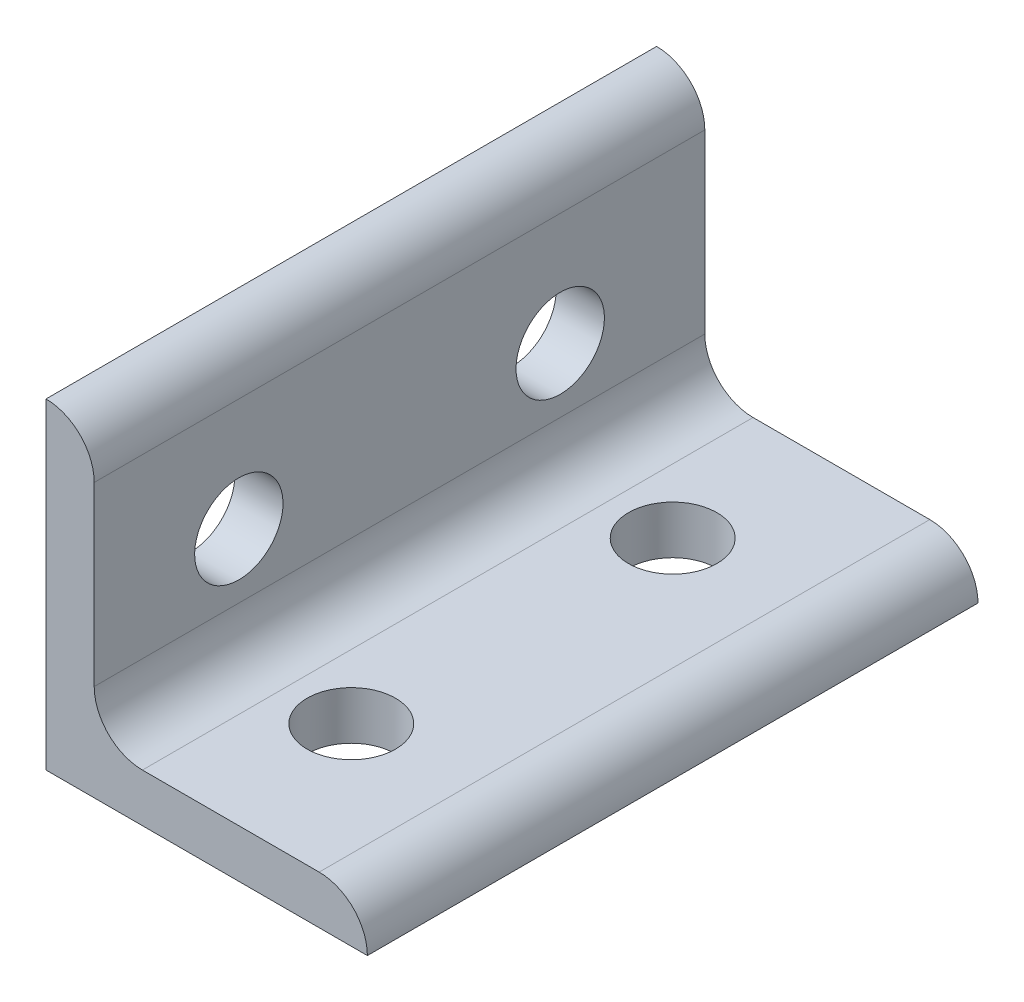
SolidWorks part; units mm, degrees
ref_plane "Front Plane" through (0, 0, 0) normal (0, 0, 1) x (1, 0, 0)
ref_plane "Top Plane" through (0, 0, 0) normal (0, 1, 0) x (1, 0, 0)
ref_plane "Right Plane" through (0, 0, 0) normal (1, 0, 0) x (0, 0, -1)
sketch "Sketch1" plane through (0, 0, 0) normal (0, 0, 1) x (1, 0, 0)
  line L0 (0, 0) -> (0, 20)
  line L1 (3, 17) -> (3, 20) construction
  line L2 (3, 17) -> (3, 6)
  line L3 (6, 3) -> (17, 3)
  line L4 (3, 20) -> (0, 20) construction
  line L5 (20, 0) -> (0, 0)
  line L6 (17, 3) -> (20, 3) construction
  line L7 (20, 3) -> (20, 0) construction
  arc A0 (3, 17) -> (0, 20) centre (0, 17) ccw
  arc A1 (20, 0) -> (17, 3) centre (17, 0) ccw
  arc A2 (3, 6) -> (6, 3) centre (6, 6) ccw
  point P10 (3, 18.5)
  dimension "E" = 3
  dimension "D" = 3
  dimension "C" = 20
  dimension "B" = 20
extrude "Boss-Extrude1" add sketch "Sketch1" along normal mid plane 38
sketch "Sketch2" plane through (0, 0, 0) normal (0, 1, 0) x (1, 0, 0)
  line L0 (0, -10) -> (10, -10) construction
  line L1 (0, -19) -> (0, -10) construction
  line L2 (10, -10) -> (10, 10) construction
  line L3 (0, -10) -> (0, 10) construction
  line L4 (0, 10) -> (10, 10) construction
  circle A0 centre (10, -10) radius 2.75
  circle A1 centre (10, 10) radius 2.75
extrude "Cut-Extrude1" cut sketch "Sketch2" along normal through all
sketch "Sketch3" plane through (0, 0, 0) normal (1, 0, 0) x (0, 0, -1)
  line L0 (-10, 0) -> (-10, 10) construction
  line L1 (-10, 10) -> (10, 10) construction
  line L2 (10, 10) -> (10, 0) construction
  line L3 (10, 0) -> (-10, 0) construction
  circle A0 centre (-10, 10) radius 2.75
  circle A1 centre (10, 10) radius 2.75
  dimension "D1" = 10
extrude "Cut-Extrude2" cut sketch "Sketch3" along normal through all
equation "\"E@Sketch3\" = \"E@Sketch2\""
equation "\"D1@Sketch3\" = \"D1@Sketch2\""
